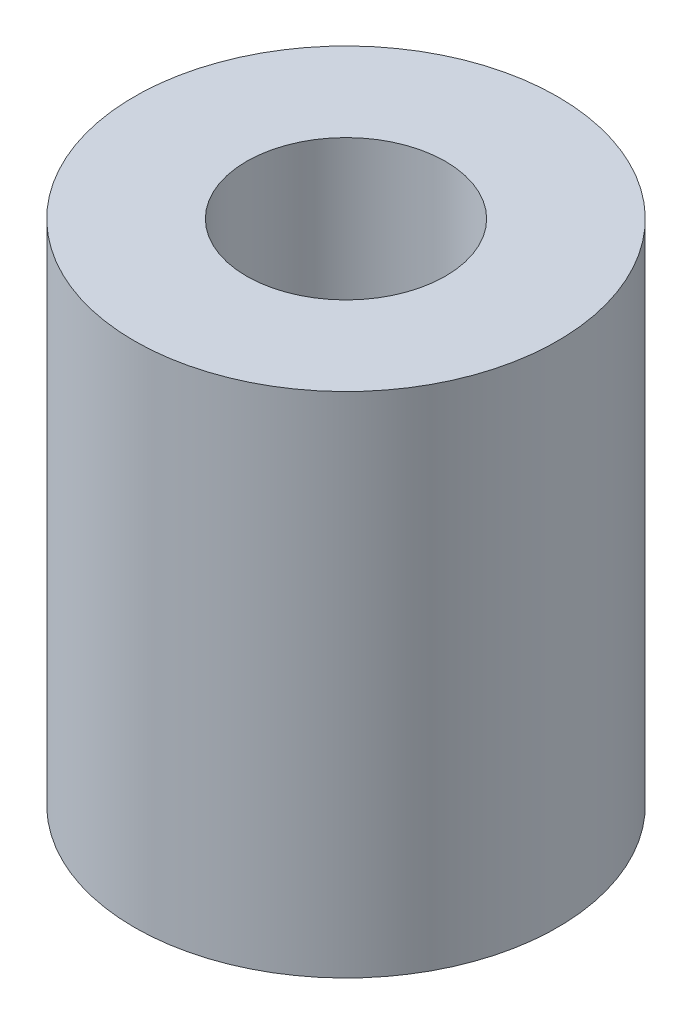
SolidWorks part; units mm, degrees
ref_plane "Front Plane" through (0, 0, 0) normal (0, 0, 1) x (1, 0, 0)
ref_plane "Top Plane" through (0, 0, 0) normal (0, 1, 0) x (1, 0, 0)
ref_plane "Right Plane" through (0, 0, 0) normal (1, 0, 0) x (0, 0, -1)
sketch "Sketch1" plane through (0, 0, 0) normal (0, 1, 0) x (1, 0, 0)
  circle A0 centre (0, 0) radius 2.35
  circle A1 centre (0, 0) radius 5
  dimension "D1" = 4.7
  dimension "D2" = 10
extrude "Boss-Extrude1" add sketch "Sketch1" along normal blind 12 contours A1 A0 | A0
sketch "Sketch2" plane through (0, 12, 0) normal (0, 1, 0) x (1, 0, 0)
  circle A0 centre (0, 0) radius 2.35 construction
  circle A1 centre (0, 0) radius 2.35
extrude "Cut-Extrude1" cut sketch "Sketch2" against normal blind 9
